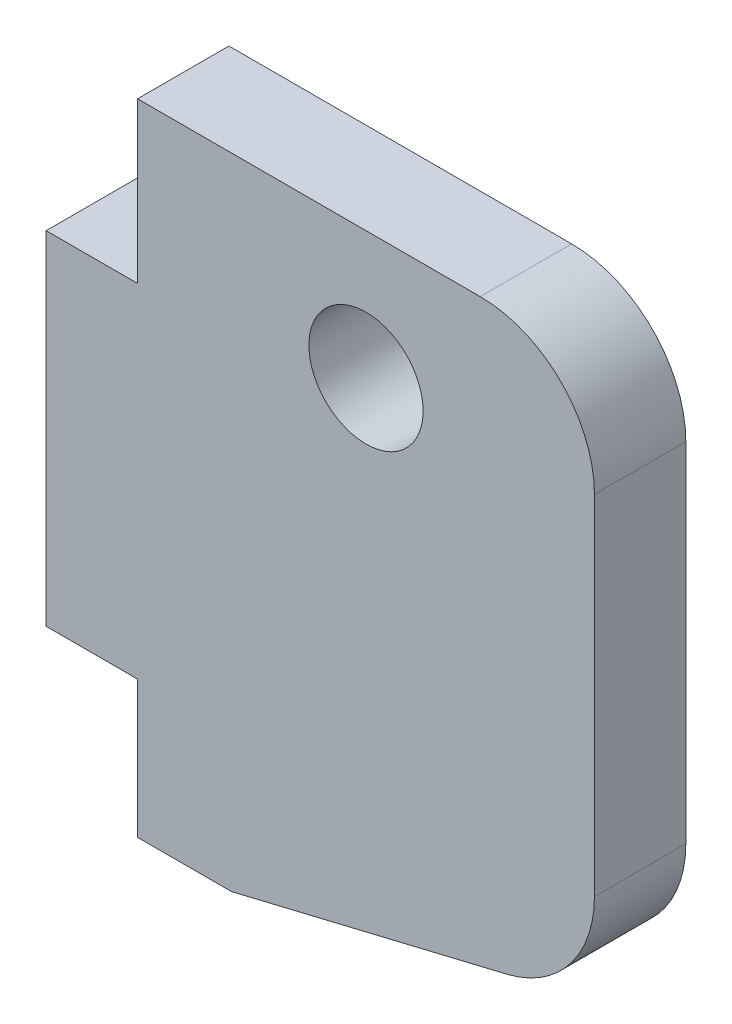
SolidWorks part; units mm, degrees
material "ﾊﾞﾙｻ"
ref_plane "正面" through (0, 0, 0) normal (0, 0, 1) x (1, 0, 0)
ref_plane "平面" through (0, 0, 0) normal (0, 1, 0) x (1, 0, 0)
ref_plane "右側面" through (0, 0, 0) normal (1, 0, 0) x (0, 0, -1)
sketch "ｽｹｯﾁ1" plane through (0, 0, 0) normal (0, 0, 1) x (1, 0, 0)
  line L0 (0, 0) -> (0, 15)
  line L1 (0, 15) -> (4, 15)
  line L2 (4, 15) -> (4, 22)
  line L3 (4, 22) -> (24, 22)
  line L4 (24, 22) -> (24, -6)
  line L5 (24, -6) -> (4, -6)
  line L6 (4, -6) -> (4, 0)
  line L7 (4, 0) -> (0, 0)
  line L8 (14, 22) -> (14, -6) construction
  line L9 (4, 22) -> (24, 8.3124) construction
  line L10 (8.1108, -6) -> (24, -2.1832)
  circle A0 centre (14, 16.41) radius 2.5
  dimension "D6" = 5
  dimension "D7" = 22.41
  dimension "D1" = 15
  dimension "D2" = 6
  dimension "D3" = 7
  dimension "D4" = 4
  dimension "D5" = 20
extrude "ﾎﾞｽ - 押し出し1" add sketch "ｽｹｯﾁ1" along normal blind 4 contours L5 L10 L4 L3 L2 L1 L0 L7 L6 A0
fillet "ﾌｨﾚｯﾄ1" radius 5 2 edges at (24, -2.1832, 2) (24, 22, 2)
